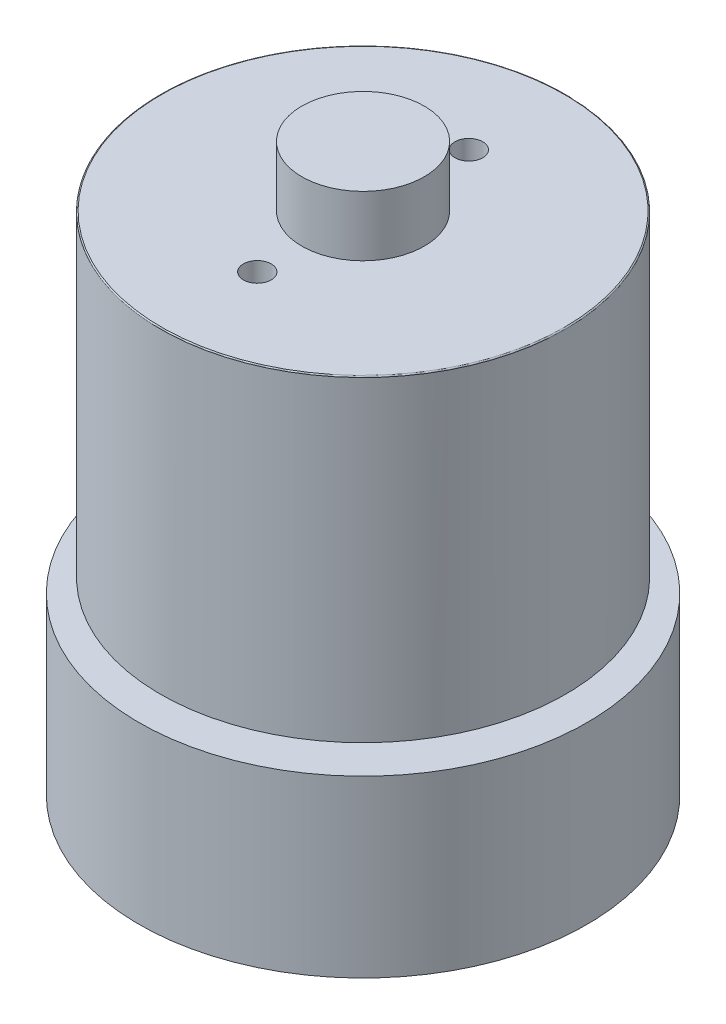
SolidWorks part; units mm, degrees
ref_plane "Front Plane" through (0, 0, 0) normal (0, 0, 1) x (1, 0, 0)
ref_plane "Top Plane" through (0, 0, 0) normal (0, 1, 0) x (1, 0, 0)
ref_plane "Right Plane" through (0, 0, 0) normal (1, 0, 0) x (0, 0, -1)
sketch "Sketch1" plane through (0, 0, 0) normal (0, 0, 1) x (1, 0, 0)
  line L0 (0, 0) -> (20.115, 0)
  line L1 (20.115, 0) -> (20.115, 15.7)
  line L2 (20.115, 15.7) -> (10.115, 15.7)
  line L3 (10.115, 15.7) -> (10.115, 16.95)
  line L4 (10.115, 16.95) -> (18.2, 16.95)
  line L5 (18.2, 16.95) -> (18.2, 45.45)
  line L6 (18.2, 45.45) -> (5.5, 45.45)
  line L7 (5.5, 45.45) -> (5.5, 50.85)
  line L8 (5.5, 50.85) -> (0, 50.85)
  line L9 (0, 50.85) -> (0, 0)
  dimension "D1" = 5.5
  dimension "D2" = 18.2
  dimension "D3" = 29.75
  dimension "D4" = 5.4
  dimension "D5" = 15.7
  dimension "D6" = 20.115
  dimension "D7" = 1.25
  dimension "D8" = 10
revolve "Revolve1" add sketch "Sketch1" angle 360 about L9
sketch "Sketch3" plane through (0, 0, 0) normal (0, -1, 0) x (1, 0, 0)
  line L0 (0, 0) -> (16, 0) construction
  line L1 (0, 0) -> (-16, 0) construction
  point P5 (-16, 0)
  point P6 (16, 0)
  dimension "D1" = 32
sketch "Sketch4" plane through (0, 45.45, 0) normal (0, 1, 0) x (1, 0, 0)
  line L0 (0, 0) -> (0, 9.5) construction
  line L1 (0, 0) -> (0, -9.5) construction
  point P4 (0, 9.5)
  point P7 (0, -9.5)
  dimension "D1" = 19
hole_wizard "M3x0.5 Tapped Hole1" positions "3DSketch1" profile "Sketch5" tap size "M3x0.5" standard "ANSI Metric"
sketch3d "3DSketch1"
  point P0 (0, 45.45, -9.5)
  point P3 (0, 45.45, 9.5)
  point P6 (-16, 0, 0)
  point P9 (16, 0, 0)
sketch "Sketch5" plane through (0, 45.45, -9.5) normal (1, 0, 0) x (0, 0, 1)
  line L0 (0, 0) -> (0, 5.7511)
  line L1 (0, 5.7511) -> (1.25, 5)
  line L2 (1.25, 5) -> (1.25, 0)
  line L5 (1.25, 0) -> (0, 0)
  line L10 (0, 5.7511) -> (-1.25, 5) construction
  line L11 (0, -6.35) -> (0, 107.95) construction
  dimension "Tap Drill Dia." = 2.5
  dimension "Tap Drill Depth" = 5
  dimension "Drill Angle" = 118
cosmetic thread "Hole Thread1" parameters "D1"=6, "D2"=3
cosmetic thread "Hole Thread2" parameters "D1"=6, "D2"=3
cosmetic thread "Hole Thread3" parameters "D1"=6, "D2"=3
cosmetic thread "Hole Thread4" parameters "D1"=6, "D2"=3
fillet "Fillet1" radius 0.1 1 edges at (-18.2, 45.45, 0)
